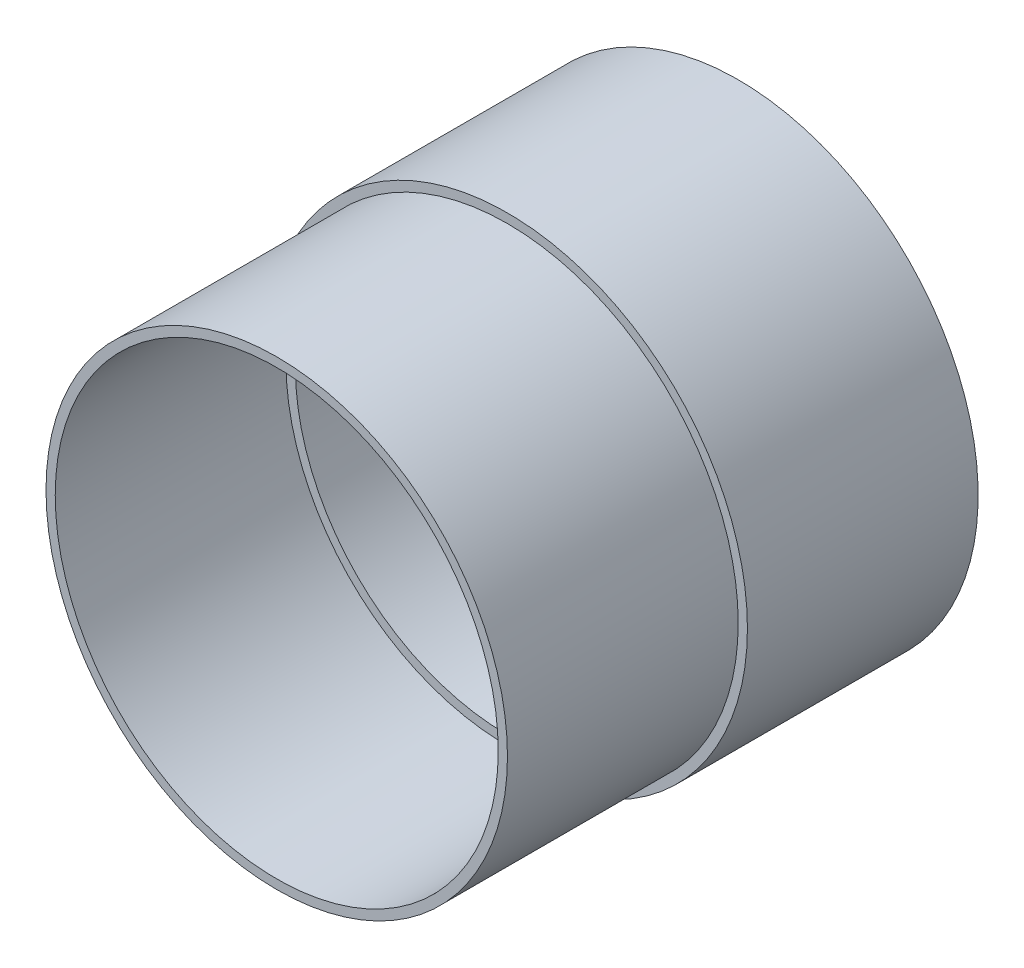
SolidWorks part; units mm, degrees
ref_plane "Alzado" through (0, 0, 0) normal (0, 0, 1) x (1, 0, 0)
ref_plane "Planta" through (0, 0, 0) normal (0, 1, 0) x (1, 0, 0)
ref_plane "Vista lateral" through (0, 0, 0) normal (1, 0, 0) x (0, 0, -1)
sketch "Croquis1" plane through (0, 0, 0) normal (0, 0, 1) x (1, 0, 0)
  circle A0 centre (-84.0183, 0) radius 50
  dimension "D1" = 100
extrude "Saliente-Extruir1" add sketch "Croquis1" along normal mid plane 100
sketch "Croquis2" plane through (0, 0, -50) normal (0, 0, -1) x (-1, 0, 0)
  circle A0 centre (84.0183, 0) radius 52
  dimension "D1" = 104
extrude "Saliente-Extruir2" add sketch "Croquis2" against normal blind 10
sketch "Croquis3" plane through (0, 0, 50) normal (0, 0, 1) x (1, 0, 0)
  circle A0 centre (-84.0183, 0) radius 48
  dimension "D1" = 96
extrude "Cortar-Extruir1" cut sketch "Croquis3" against normal blind 97
sketch "Croquis4" plane through (0, 0, 0) normal (0, 0, 1) x (1, 0, 0)
  circle A0 centre (-84.0183, 0) radius 52
extrude "Saliente-Extruir3" add sketch "Croquis4" against normal blind 47
sketch "Croquis5" plane through (0, 0, 0) normal (0, 0, 1) x (1, 0, 0)
  circle A0 centre (-84.0183, 0) radius 45.9662
extrude "Cortar-Extruir2" cut sketch "Croquis5" against normal blind 47
